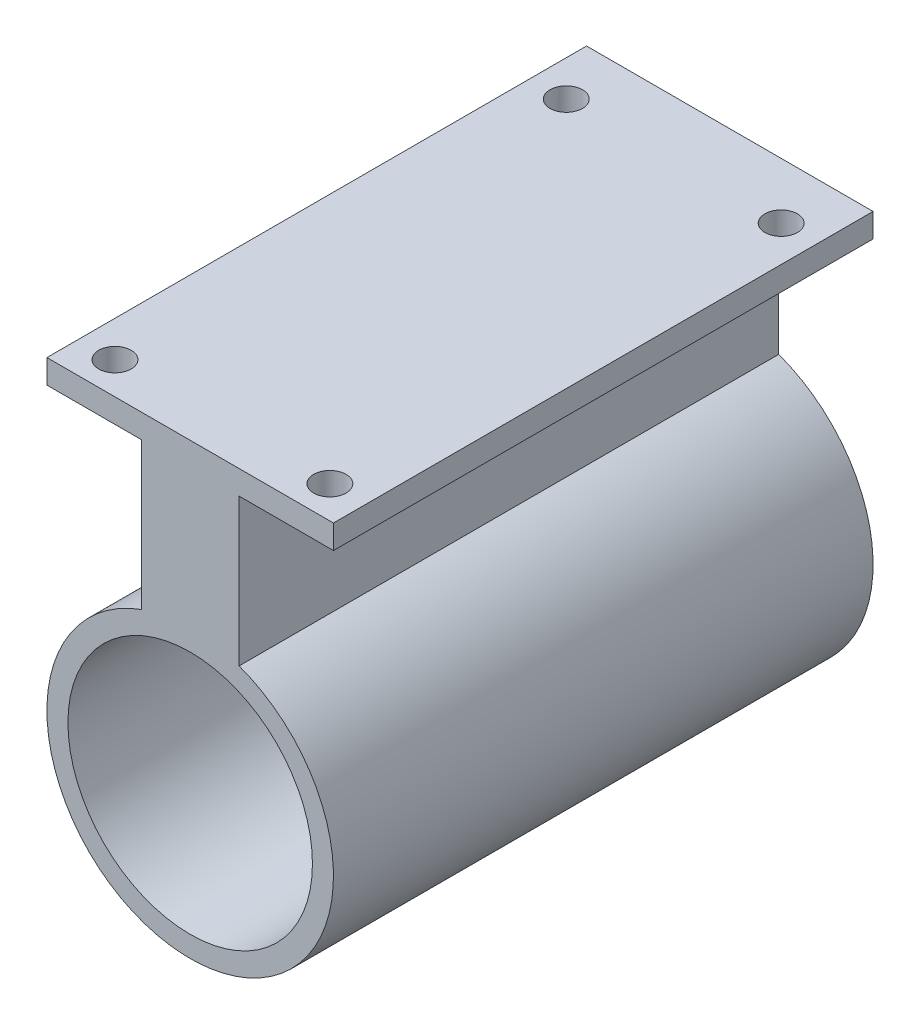
SolidWorks part; units mm, degrees
ref_plane "Alzado" through (0, 0, 0) normal (0, 0, 1) x (1, 0, 0)
ref_plane "Planta" through (0, 0, 0) normal (0, 1, 0) x (1, 0, 0)
ref_plane "Vista lateral" through (0, 0, 0) normal (1, 0, 0) x (0, 0, -1)
sketch "Croquis1" plane through (0, 0, 0) normal (0, 0, 1) x (1, 0, 0)
  line L0 (-5.1199, -1.25) -> (-15, -1.25)
  line L1 (15, -1.25) -> (5.1199, -1.25)
  line L2 (15, -1.25) -> (15, 1.25)
  line L3 (15, 1.25) -> (-15, 1.25)
  line L4 (-15, -1.25) -> (-15, 1.25)
  line L5 (15, -1.25) -> (-15, 1.25) construction
  line L6 (15, 1.25) -> (-15, -1.25) construction
  line L7 (-5.1199, -13.25) -> (-5.1199, -16.6508)
  line L8 (5.1199, -13.25) -> (5.1199, -1.25)
  line L9 (5.1199, -13.25) -> (5.1199, -16.6508)
  line L10 (-5.1199, -13.25) -> (-5.1199, -1.25)
  line L11 (5.1199, -13.25) -> (-5.1199, -1.25) construction
  line L12 (5.1199, -1.25) -> (-5.1199, -13.25) construction
  arc A0 (-5.1199, -16.6508) -> (5.1199, -16.6508) centre (0, -30.75) ccw
  circle A1 centre (0, -30.75) radius 12.5
  point P0 (0, 0)
  point P6 (0, -7.25)
  point P13 (0, -15.75)
  dimension "D1" = 30
  dimension "D2" = 2.5
  dimension "D3" = 12
  dimension "D4" = 32
extrude "Saliente-Extruir1" add sketch "Croquis1" along normal blind 54
sketch "Croquis2" plane through (0, 0, 0) normal (0, 0, -1) x (-1, 0, 0)
  circle A0 centre (0, -30.75) radius 15
extrude "Saliente-Extruir2" add sketch "Croquis2" along normal blind 2.5
sketch "Croquis3" plane through (0, 0, -2.5) normal (0, 0, -1) x (-1, 0, 0)
  circle A0 centre (0, -30.75) radius 3.75
extrude "Cortar-Extruir2" cut sketch "Croquis3" against normal blind 2.5
sketch "Croquis5" plane through (0, 0, -2.5) normal (0, 0, -1) x (-1, 0, 0)
  line L1 (0, -22.25) -> (0, -39.25) construction
  line L2 (0, -39.25) -> (0, -22.25)
  circle A1 centre (0, -22.25) radius 1.5
  circle A2 centre (0, -39.25) radius 1.5
  point P10 (0, -30.75)
extrude "Cortar-Extruir3" cut sketch "Croquis5" against normal blind 2.5
sketch "Croquis9" plane through (0, 1.25, 0) normal (0, 1, 0) x (1, 0, 0)
  line L0 (0, 0) -> (0, -54) construction
  line L1 (15, -54) -> (-15, -54) construction
  line L2 (-15, -27) -> (15, -27) construction
  line L3 (-15, -54) -> (-15, 0) construction
  line L4 (15, -54) -> (15, 0) construction
  line L5 (0, -27) -> (-15, -54) construction
  line L6 (-7.5, -40.5) -> (-7.5, -54) construction
  line L7 (-7.5, -47.25) -> (-15, -54) construction
  circle A0 centre (-11.25, -50.625) radius 1.5
  circle A1 centre (-11.25, -3.375) radius 1.5
  circle A2 centre (11.25, -50.625) radius 1.5
  circle A3 centre (11.25, -3.375) radius 1.5
  dimension "D1" = 47.25
  dimension "D5" = 3
  dimension "D2" = 22.5
  dimension "D3" = 54
  dimension "D4" = 30
extrude "Cortar-Extruir5" cut sketch "Croquis9" against normal blind 2.5
sketch "Croquis10" plane through (0, 0, 0) normal (0, 0, -1) x (-1, 0, 0)
  line L0 (0, -15.75) -> (0, 1.25) construction
  line L1 (-15, 1.25) -> (15, 1.25) construction
  line L2 (-15, 1.25) -> (15, 1.25)
  line L3 (15, 1.25) -> (15, -1.25)
  line L4 (15, -1.25) -> (5.1199, -1.25)
  line L5 (5.1199, -1.25) -> (5.1199, -16.6508)
  line L6 (-15, 1.25) -> (-15, -1.25)
  line L7 (-15, -1.25) -> (-5.1199, -1.25)
  line L8 (-5.1199, -1.25) -> (-5.1199, -16.6508)
  arc A0 (5.1199, -16.6508) -> (-5.1199, -16.6508) centre (0, -30.75) ccw construction
  arc A1 (-5.1199, -16.6508) -> (5.1199, -16.6508) centre (0, -30.75) cw
extrude "Saliente-Extruir3" add sketch "Croquis10" along normal blind 2.5
sketch "Croquis11" plane through (0, 0, 54) normal (0, 0, 1) x (1, 0, 0)
  circle A0 centre (0, -30.75) radius 12.8
extrude "Cortar-Extruir6" cut sketch "Croquis11" against normal blind 54
sketch "Croquis12" plane through (0, 0, -2.5) normal (0, 0, -1) x (-1, 0, 0)
  circle A3 centre (0, -22.25) radius 1.7
  circle A4 centre (0, -39.25) radius 1.7
extrude "Cortar-Extruir7" cut sketch "Croquis12" against normal blind 2.5
sketch "Croquis13" plane through (0, 0, -2.5) normal (0, 0, -1) x (-1, 0, 0)
  line L0 (-1.7, -22.25) -> (1.7, -22.25) construction
  line L1 (-3.75, -30.75) -> (3.75, -30.75) construction
  line L2 (-1.7, -39.25) -> (1.7, -39.25) construction
  line L3 (-5.1199, -1.25) -> (-5.1199, -16.6508) construction
  circle A0 centre (0, -22.25) radius 1.7 construction
  circle A1 centre (0, -30.75) radius 3.75 construction
  circle A2 centre (0, -39.25) radius 1.7 construction
  dimension "D1" = 3.4
  dimension "D2" = 7.5
  dimension "D3" = 3.4
  dimension "D4" = 15.4008
sketch "Croquis14" plane through (0, 1.25, 0) normal (0, 1, 0) x (1, 0, 0)
  line L0 (-11.25, -4.875) -> (-11.25, -1.875) construction
  circle A0 centre (-11.25, -3.375) radius 1.5 construction
  circle A1 centre (-11.25, -3.375) radius 1.8
  dimension "D1" = 3.6
sketch "Croquis16" plane through (0, 1.25, 0) normal (0, 1, 0) x (1, 0, 0)
  circle A0 centre (-11.25, -3.375) radius 1.7
extrude "Cortar-Extruir8" cut sketch "Croquis16" against normal blind 2.5
sketch "Croquis17" plane through (0, 1.25, 0) normal (0, 1, 0) x (1, 0, 0)
  line L0 (-11.25, -1.675) -> (-11.25, -5.075) construction
  line L1 (0, 2.5) -> (0, -54) construction
  line L2 (1.7, 2.5) -> (-1.7, 2.5) construction
  line L3 (15, -54) -> (-15, -54) construction
  circle A0 centre (-11.25, -3.375) radius 1.7 construction
  circle A1 centre (-11.25, -3.375) radius 1.7
  circle A2 centre (11.25, -3.375) radius 1.7
  circle A3 centre (-11.25, -50.625) radius 1.7
  circle A4 centre (11.25, -50.625) radius 1.7
  dimension "D1" = 3.4
extrude "Cortar-Extruir9" cut sketch "Croquis17" against normal blind 2.5
sketch "Croquis18" plane through (0, 1.25, 0) normal (0, 1, 0) x (1, 0, 0)
  line L0 (-11.25, -1.675) -> (-11.25, -5.075) construction
  line L1 (-11.25, -48.925) -> (-11.25, -52.325) construction
  circle A0 centre (-11.25, -3.375) radius 1.7 construction
  circle A1 centre (-11.25, -50.625) radius 1.7 construction
sketch "Croquis19" plane through (0, 0, -2.5) normal (0, 0, -1) x (-1, 0, 0)
  line L0 (0, -23.95) -> (0, -20.55) construction
  circle A0 centre (0, -22.25) radius 1.7 construction
